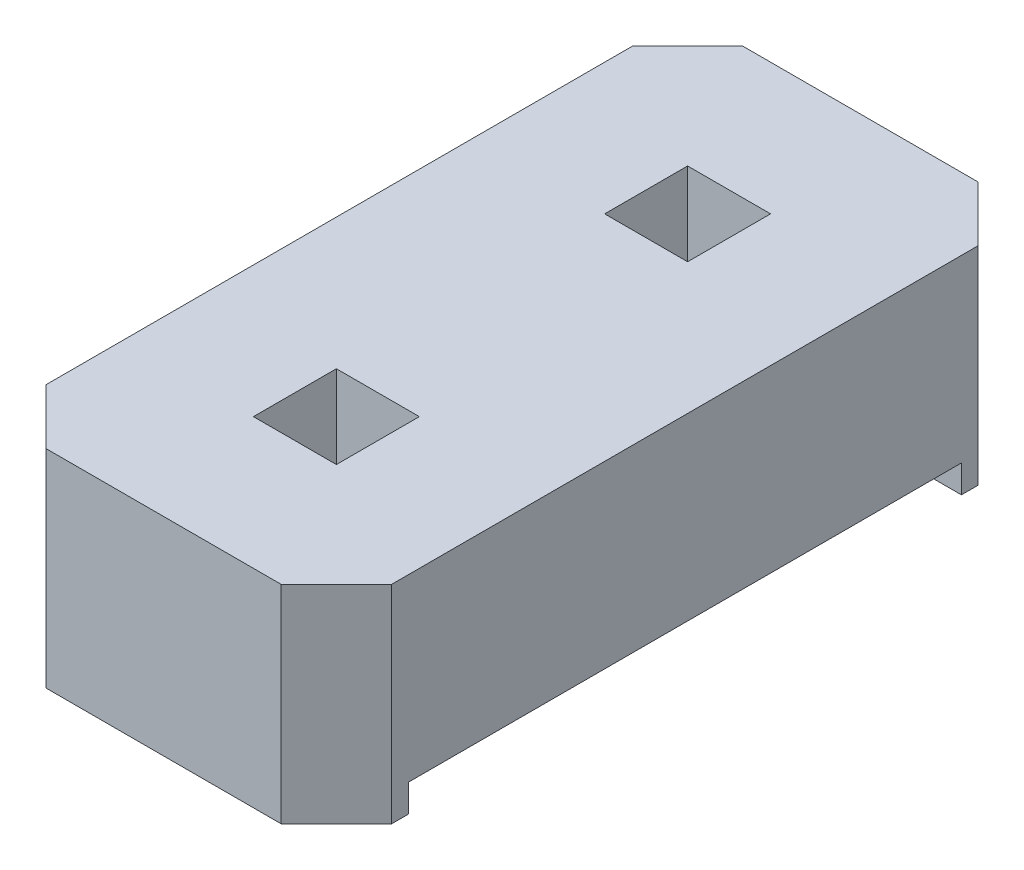
SolidWorks part; units mm, degrees
ref_plane "Plan de face" through (0, 0, 0) normal (0, 0, 1) x (1, 0, 0)
ref_plane "Plan de dessus" through (0, 0, 0) normal (0, 1, 0) x (1, 0, 0)
ref_plane "Plan de droite" through (0, 0, 0) normal (1, 0, 0) x (0, 0, -1)
sketch "Esquisse1" plane through (0, 0, 0) normal (0, 1, 0) x (1, 0, 0)
  line L0 (-1.25, 2.12) -> (-0.85, 2.52)
  line L1 (-0.85, -2.52) -> (0.85, -2.52)
  line L2 (-1.25, -2.12) -> (-1.25, 2.12)
  line L3 (-0.85, 2.52) -> (0.85, 2.52)
  line L4 (1.25, -2.12) -> (1.25, 2.12)
  line L5 (-1.25, -2.52) -> (1.25, 2.52) construction
  line L6 (-1.25, 2.52) -> (1.25, -2.52) construction
  line L7 (0.85, 2.52) -> (1.25, 2.12)
  line L8 (0.85, -2.52) -> (1.25, -2.12)
  line L9 (-1.25, -2.12) -> (-0.85, -2.52)
  line L10 (0.3, -0.97) -> (-0.3, -1.57) construction
  line L11 (0.3, -0.97) -> (-0.3, -0.97)
  line L12 (0.3, -0.97) -> (0.3, -1.57)
  line L13 (0.3, -1.57) -> (-0.3, -1.57)
  line L14 (-0.3, -0.97) -> (-0.3, -1.57)
  line L15 (1.25, 0) -> (-1.25, 0) construction
  line L16 (0.3, 0.97) -> (0.3, 1.57)
  line L17 (0.3, 1.57) -> (-0.3, 1.57)
  line L18 (-0.3, 0.97) -> (-0.3, 1.57)
  line L19 (0.3, 0.97) -> (-0.3, 0.97)
  point P0 (0, 0)
  point P14 (0, 0)
  point P19 (0, -1.27)
  dimension "D1" = 2.5
  dimension "D2" = 5.04
  dimension "D3" = 0.6
  dimension "D4" = 2.54
extrude "Boss.-Extru.1" add sketch "Esquisse1" along normal blind 1.5
sketch "Esquisse2" plane through (-1.25, 0, 0) normal (-1, 0, 0) x (0, 0, 1)
  line L2 (-2, -0.2) -> (2, -0.2)
  line L3 (-2, -0.2) -> (-2, 0.2)
  line L4 (-2, 0.2) -> (2, 0.2)
  line L5 (2, -0.2) -> (2, 0.2)
  line L6 (-2, -0.2) -> (2, 0.2) construction
  line L7 (-2, 0.2) -> (2, -0.2) construction
  point P0 (0, 0)
  dimension "D1" = 0.2
  dimension "D2" = 4
extrude "Enlèv. mat.-Extru.1" cut sketch "Esquisse2" against normal through all
